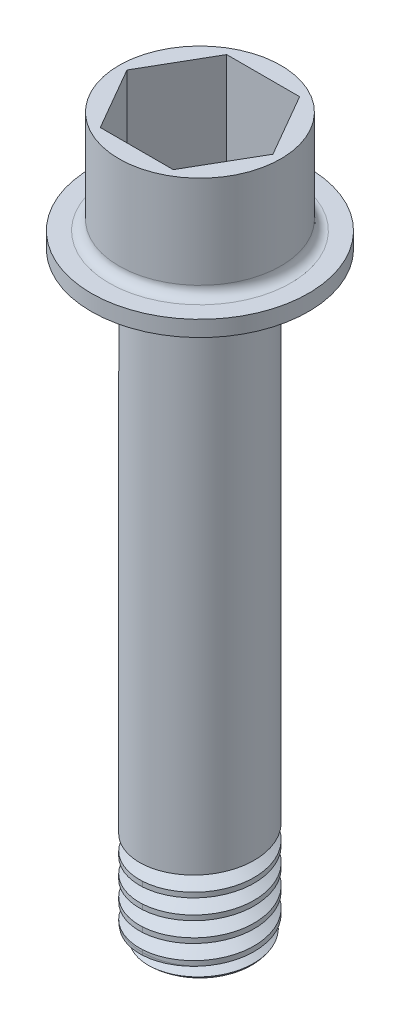
SolidWorks part; units mm, degrees
ref_plane "Plano frontal" through (0, 0, 0) normal (0, 0, 1) x (1, 0, 0)
ref_plane "Plano superior" through (0, 0, 0) normal (0, 1, 0) x (1, 0, 0)
ref_plane "Plano direito" through (0, 0, 0) normal (1, 0, 0) x (0, 0, -1)
sketch "Esboço1" plane through (0, 0, 0) normal (0, 1, 0) x (1, 0, 0)
  circle A0 centre (0, 0) radius 5.82
  dimension "D1" = 11.64
extrude "Ressalto-extrusão1" add sketch "Esboço1" along normal blind 60.8
sketch "Esboço2" plane through (0, 60.8, 0) normal (0, 1, 0) x (1, 0, 0)
  circle A0 centre (0, 0) radius 11
  dimension "D1" = 22
extrude "Ressalto-extrusão2" add sketch "Esboço2" along normal blind 12 contours A0
fillet "Filete1" radius 2 1 edges at (0, 60.8, 5.82)
sketch "Esboço3" plane through (0, 72.8, 0) normal (0, 1, 0) x (1, 0, 0)
  line L0 (-11, 0) -> (11, 0) construction
  line L8 (-7.3901, 0) -> (-3.695, -6.4)
  line L9 (-3.695, -6.4) -> (3.695, -6.4)
  line L10 (3.695, -6.4) -> (7.3901, 0)
  line L11 (7.3901, 0) -> (3.695, 6.4)
  line L12 (3.695, 6.4) -> (-3.695, 6.4)
  line L13 (-3.695, 6.4) -> (-7.3901, 0)
  circle A0 centre (0, 0) radius 6.4 construction
  circle A1 centre (0, 0) radius 11 construction
  dimension "D1" = 12.8
  dimension "D2" = 60
extrude "Corte-extrusão1" cut sketch "Esboço3" against normal blind 10.4
sketch "Esboço4" plane through (0, 0, 0) normal (0, -1, 0) x (1, 0, 0)
  circle A0 centre (0, 0) radius 3.7
  dimension "D1" = 7.4
extrude "Corte-extrusão2" cut sketch "Esboço4" against normal offset from surface (61 mm away) 1.4 up to face at (0, 62.4, 0)
sketch "Esboço5" plane through (0, 62.4, 0) normal (0, 1, 0) x (1, 0, 0)
  circle A0 centre (0, 0) radius 2
  dimension "D1" = 4
extrude "Corte-extrusão3" cut sketch "Esboço5" against normal blind 2
sketch "Esboço8" plane through (0, 0, 0) normal (0, -1, 0) x (1, 0, 0)
  circle A0 centre (0, 0) radius 5.82 construction
  circle A1 centre (0, 0) radius 5.82
fillet "Filete2" radius 2 1 edges at (0, 0, 5.82)
curve "Hélice/Espiral1" pitch 2 height 10.4 turns 5.2
sketch "Esboço9" plane through (0, 0, 0) normal (1, 0, 0) x (0, 0, -1)
  line L1 (5.82, 0) -> (5.8198, 0) construction
  line L5 (5.82, 2) -> (5.82, 58.8) construction
  line L6 (4.5198, 0) -> (6.4698, -1.1258)
  line L7 (6.4698, -1.1258) -> (6.4698, 1.1258)
  line L8 (6.4698, 1.1258) -> (4.5198, 0)
  circle A0 centre (5.8198, 0) radius 0.65 construction
  spline S1 degree 3 poles (5.82, 0) (5.82, 0.0415) (5.5155, 0.1254) (4.215, 0.2506) (2.2698, 0.3759) (-0.0226, 0.5012) (-2.3116, 0.6265) (-4.2469, 0.7518) (-5.5327, 0.8771) (-5.9721, 1.0024) (-5.498, 1.1277) (-4.1829, 1.253) (-2.2279, 1.3783) (0.0678, 1.5036) (2.3532, 1.6289) (4.2786, 1.7542) (5.5495, 1.8795) (5.9716, 2.0048) (5.4802, 2.1301) (4.1505, 2.2554) (2.1859, 2.3807) (-0.113, 2.506) (-2.3947, 2.6313) (-4.31, 2.7566) (-5.5661, 2.8819) (-5.9707, 3.0072) (-5.462, 3.1325) (-4.1179, 3.2578) (-2.1438, 3.3831) (0.1582, 3.5084) (2.436, 3.6337) (4.3412, 3.759) (5.5823, 3.8843) (5.9695, 4.0096) (5.4436, 4.1349) (4.085, 4.2602) (2.1015, 4.3855) (-0.2034, 4.5108) (-2.4772, 4.6361) (-4.3721, 4.7614) (-5.5982, 4.8867) (-5.968, 5.012) (-5.4248, 5.1373) (-4.0519, 5.2627) (-2.0591, 5.388) (0.2486, 5.5133) (2.5183, 5.6386) (4.4028, 5.7639) (5.6138, 5.8892) (5.9661, 6.0145) (5.4058, 6.1398) (4.0186, 6.2651) (2.0166, 6.3904) (-0.2938, 6.5157) (-2.5592, 6.641) (-4.4332, 6.7663) (-5.6291, 6.8916) (-5.9639, 7.0169) (-5.3864, 7.1422) (-3.985, 7.2675) (-1.974, 7.3928) (0.3389, 7.5181) (2.6, 7.6434) (4.4634, 7.7687) (5.644, 7.894) (5.9613, 8.0193) (5.3667, 8.1446) (3.9512, 8.2699) (1.9313, 8.3952) (-0.384, 8.5205) (-2.6406, 8.6458) (-4.4933, 8.7711) (-5.6586, 8.8964) (-5.9584, 9.0217) (-5.3467, 9.147) (-3.9172, 9.2723) (-1.8885, 9.3976) (0.4291, 9.5229) (2.6811, 9.6482) (4.523, 9.7735) (5.6729, 9.8988) (5.9553, 10.0241) (5.3259, 10.1494) (3.8851, 10.2746) (2.5201, 10.3585) (1.7985, 10.4) knots 0 0 0 0 0.012048 0.024096 0.036145 0.048193 0.060241 0.072289 0.084337 0.096386 0.108434 0.120482 0.13253 0.144578 0.156627 0.168675 0.180723 0.192771 0.204819 0.216867 0.228916 0.240964 0.253012 0.26506 0.277108 0.289157 0.301205 0.313253 0.325301 0.337349 0.349398 0.361446 0.373494 0.385542 0.39759 0.409639 0.421687 0.433735 0.445783 0.457831 0.46988 0.481928 0.493976 0.506024 0.518072 0.53012 0.542169 0.554217 0.566265 0.578313 0.590361 0.60241 0.614458 0.626506 0.638554 0.650602 0.662651 0.674699 0.686747 0.698795 0.710843 0.722892 0.73494 0.746988 0.759036 0.771084 0.783133 0.795181 0.807229 0.819277 0.831325 0.843373 0.855422 0.86747 0.879518 0.891566 0.903614 0.915663 0.927711 0.939759 0.951807 0.963855 0.975904 0.987952 1 1 1 1 construction
  dimension "D1" = 0.0002
  dimension "D2" = 1.3
sweep "Varredura de corte1" cut profiles "Esboço9" path "Hélice/Espiral1"
sketch "Esboço10" plane through (0, 72.8, 0) normal (0, 1, 0) x (1, 0, 0)
  circle A0 centre (0, 0) radius 8.2
  dimension "D1" = 16.4
extrude "Corte-extrusão4" cut sketch "Esboço10" against normal blind 10.4 flip side to cut
fillet "Filete3" radius 1 1 edges at (0, 62.4, 8.2)
sketch "Esboço12" plane through (0, 0, 0) normal (0.309, 0, -0.9511) x (-0.9511, 0, -0.309)
  line L3 (5.82, 9.6493) -> (5.82, 11.1507)
  line L4 (5.82, 11.1507) -> (4.5198, 10.4)
  line L5 (4.5198, 10.4) -> (5.82, 9.6493)
  line L6 (5.82, 9.6493) -> (5.82, 11.1507)
  line L7 (5.82, 11.1507) -> (4.5198, 10.4)
  line L8 (4.5198, 10.4) -> (5.82, 9.6493)
  dimension "D1" = 0
extrude "Corte-extrusão6" cut sketch "Esboço12" against normal blind 10
